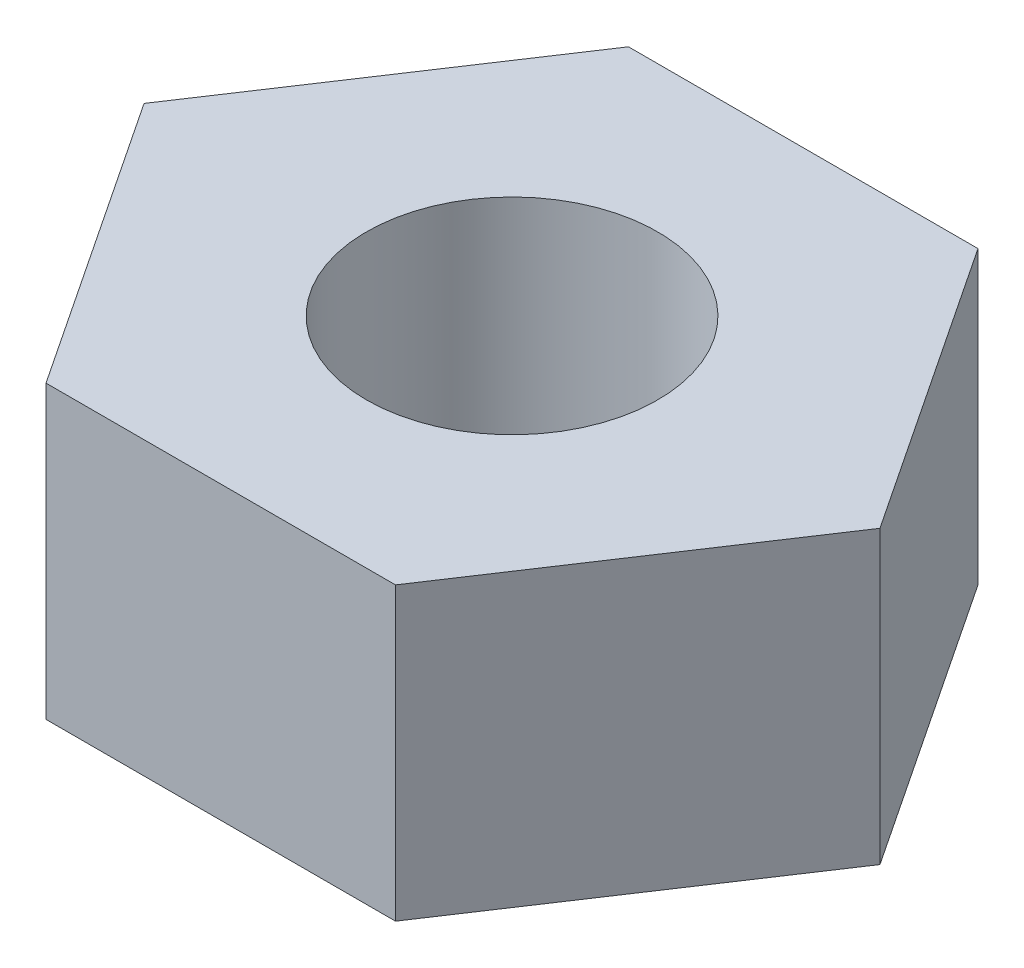
SolidWorks part; units mm, degrees
ref_plane "Front Plane" through (0, 0, 0) normal (0, 0, 1) x (1, 0, 0)
ref_plane "Top Plane" through (0, 0, 0) normal (0, 1, 0) x (1, 0, 0)
ref_plane "Right Plane" through (0, 0, 0) normal (1, 0, 0) x (0, 0, -1)
sketch "Sketch1" plane through (0, 0, 0) normal (0, 1, 0) x (1, 0, 0)
  line L0 (-6.0018, 10) -> (5.9982, 10)
  line L1 (5.9982, 10) -> (12.6315, 0)
  line L2 (12.6315, 0) -> (5.9982, -10)
  line L3 (5.9982, -10) -> (-6.0018, -10)
  line L4 (-6.0018, -10) -> (-12.635, 0)
  line L5 (-12.635, 0) -> (-6.0018, 10)
  circle A0 centre (0, 0) radius 5
  point P5 (0, 0)
  point P10 (0, 0)
  point P11 (0, 0)
  point P12 (0, 0)
  dimension "D1" = 10
  dimension "D2" = 12
  dimension "D3" = 20
  dimension "D4" = 12.635
extrude "Boss-Extrude1" add sketch "Sketch1" along normal blind 10
